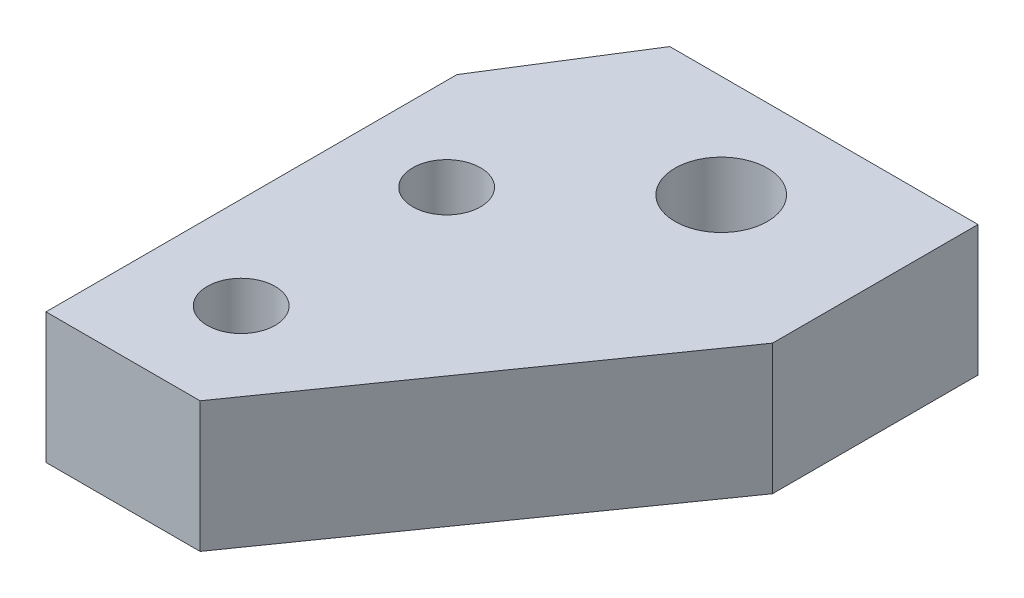
SolidWorks part; units mm, degrees
material "6061-T6 (SS)"
ref_plane "Front Plane" through (0, 0, 0) normal (0, 0, 1) x (1, 0, 0)
ref_plane "Top Plane" through (0, 0, 0) normal (0, 1, 0) x (1, 0, 0)
ref_plane "Right Plane" through (0, 0, 0) normal (1, 0, 0) x (0, 0, -1)
sketch "Sketch1" plane through (0, 0, 0) normal (0, 1, 0) x (1, 0, 0)
  line L0 (0, 0) -> (0, 20)
  line L1 (0, 20) -> (4, 26.3631)
  line L2 (4, 26.3631) -> (19, 26.3631)
  line L3 (19, 26.3631) -> (19, 16.3631)
  line L4 (19, 16.3631) -> (7.5, 0)
  line L5 (7.5, 0) -> (0, 0)
  dimension "D1" = 7.5
  dimension "D2" = 20
  dimension "D3" = 20
  dimension "D4" = 10
  dimension "D5" = 15
  dimension "D6" = 19
extrude "Boss-Extrude1" add sketch "Sketch1" along normal mid plane 6.35
hole_wizard "M4x0.7 Tapped Hole1" positions "Sketch2" profile "Sketch3" tap size "M4x0.7" standard "ANSI Metric" end condition through all
sketch "Sketch2" plane through (0, 3.175, 0) normal (0, 1, 0) x (1, 0, 0)
  point P0 (4.5, 15)
  point P3 (4.5, 5)
sketch "Sketch3" plane through (4.5, 3.175, -15) normal (1, 0, 0) x (0, 0, 1)
  line L0 (0, 0) -> (0, 6.35)
  line L1 (0, 6.35) -> (1.65, 6.35)
  line L2 (1.65, 6.35) -> (1.65, 0)
  line L5 (1.65, 0) -> (0, 0)
  line L11 (0, -6.35) -> (0, 107.95) construction
  dimension "Thru Tap Drill Dia." = 3.3
  dimension "Thru Tap Drill Depth" = 6.35
cosmetic thread "Hole Thread1"
cosmetic thread "Hole Thread2"
hole_wizard "M4 Clearance Hole1" positions "Sketch4" profile "Sketch5" hole size "M4" standard "ANSI Metric" end condition through all
sketch "Sketch4" plane through (0, 3.175, 0) normal (0, 1, 0) x (1, 0, 0)
  point P0 (11.5, 21.3645)
sketch "Sketch5" plane through (11.5, 3.175, -21.3645) normal (1, 0, 0) x (0, 0, 1)
  line L0 (0, 0) -> (0, 6.35)
  line L1 (0, 6.35) -> (2.25, 6.35)
  line L2 (2.25, 6.35) -> (2.25, 0)
  line L5 (2.25, 0) -> (0, 0)
  line L11 (0, -6.35) -> (0, 107.95) construction
  dimension "Thru Hole Dia." = 4.5
  dimension "Thru Hole Depth" = 6.35
